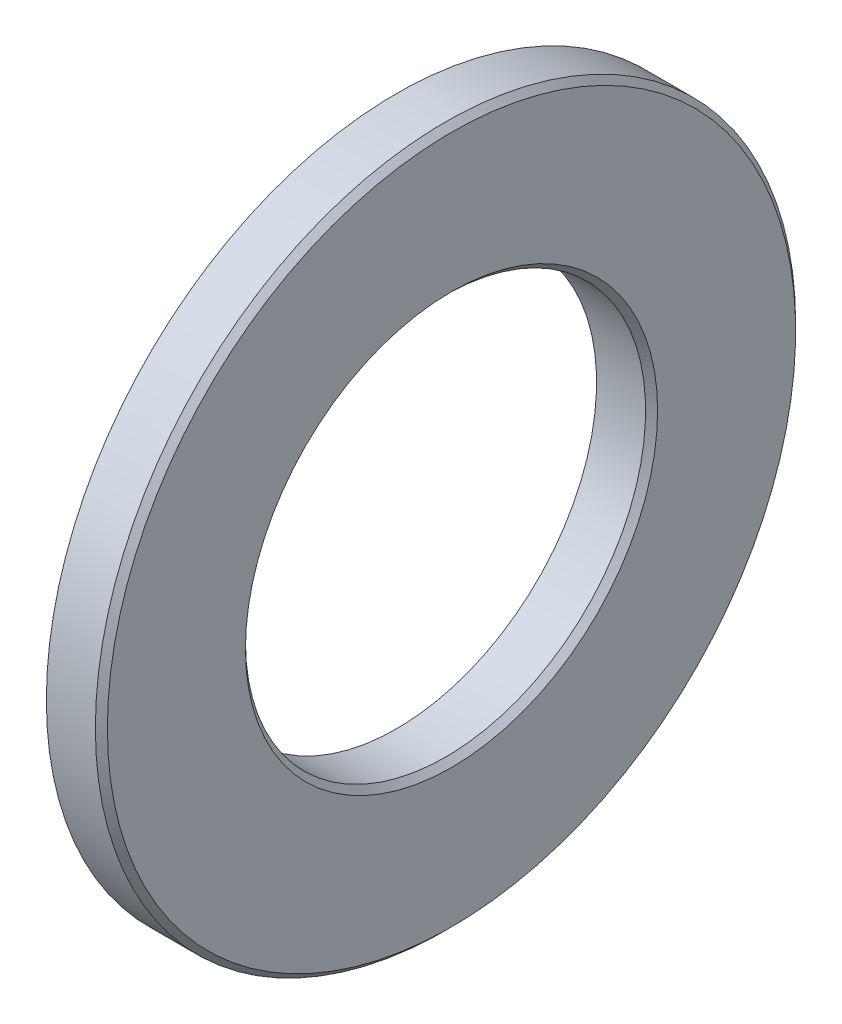
SolidWorks part; units mm, degrees
ref_plane "Front Plane" through (0, 0, 0) normal (0, 0, 1) x (1, 0, 0)
ref_plane "Top Plane" through (0, 0, 0) normal (0, 1, 0) x (1, 0, 0)
ref_plane "Right Plane" through (0, 0, 0) normal (1, 0, 0) x (0, 0, -1)
ref_plane "Plane1" through (0, 0, 0) normal (0, 0, 1) x (1, 0, 0)
sketch "Sketch1" plane through (0, 0, 0) normal (0, 0, 1) x (1, 0, 0)
  line L0 (1, 10) -> (3.45, 10)
  line L1 (3.45, 10) -> (3.75, 10.3)
  line L2 (3.75, 10.3) -> (3.75, 17.2)
  line L3 (3.75, 17.2) -> (3.45, 17.5)
  line L4 (3.45, 17.5) -> (1, 17.5)
  line L5 (1, 17.5) -> (1, 10)
  line L6 (50, 0) -> (-50, 0) construction
revolve "Revolve1" add sketch "Sketch1" angle 360 about L6
